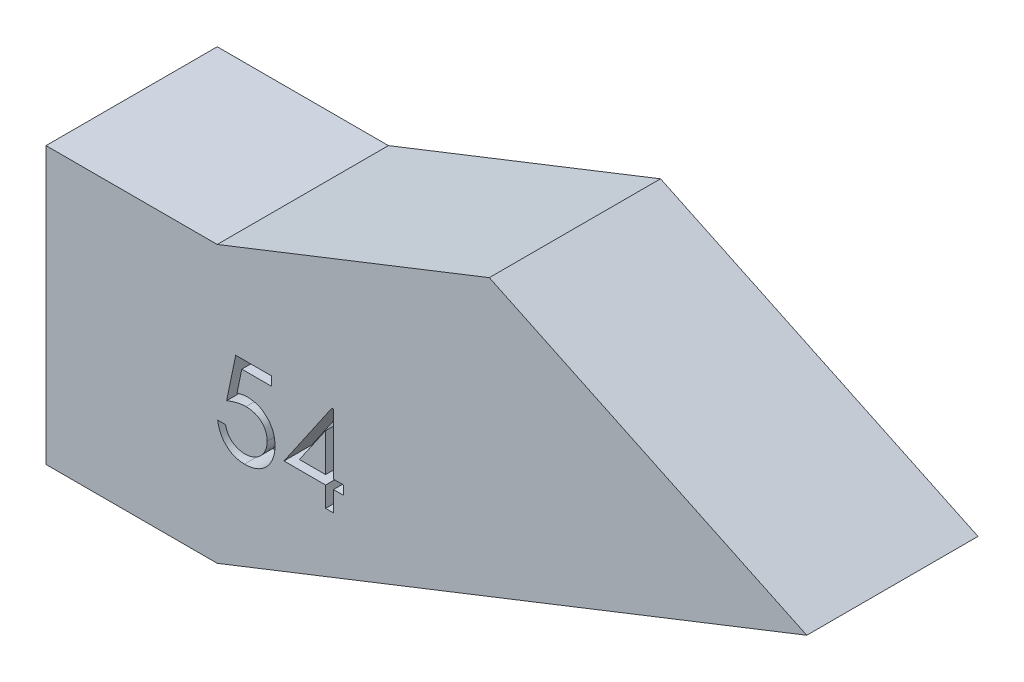
SolidWorks part; units mm, degrees
ref_plane "Front Plane" through (0, 0, 0) normal (0, 0, 1) x (1, 0, 0)
ref_plane "Top Plane" through (0, 0, 0) normal (0, 1, 0) x (1, 0, 0)
ref_plane "Right Plane" through (0, 0, 0) normal (1, 0, 0) x (0, 0, -1)
sketch "Sketch1" plane through (0, 0, 0) normal (0, 0, 1) x (-1, 0, 0)
  line L2 (-102.5471, 86.4995) -> (-91.0517, 81.0325)
  line L4 (-81.1984, 94.9179) -> (-74.9984, 94.9179)
  line L7 (-81.1984, 84.9179) -> (-74.9984, 84.9179)
  line L8 (-74.9984, 94.9179) -> (-74.9984, 84.9179)
  line L10 (-102.5385, 76.5028) -> (-81.1984, 84.9179)
  line L11 (-102.5471, 86.4995) -> (-81.1984, 94.9179)
  point P25 (-102.5385, 76.5028)
  point P26 (-102.5471, 86.4995)
  dimension "D2" = 10
  dimension "D3" = 6.2
extrude "Boss-Extrude1" add sketch "Sketch1" along normal blind 6.2 contours L11 L2 L10 L7 L8 L4
sketch "Sketch2" plane through (0, 0, 6.2) normal (0, 0, 1) x (1, 0, 0)
  text T0 "54"
extrude "Cut-Extrude1" cut sketch "Sketch2" against normal blind 1
